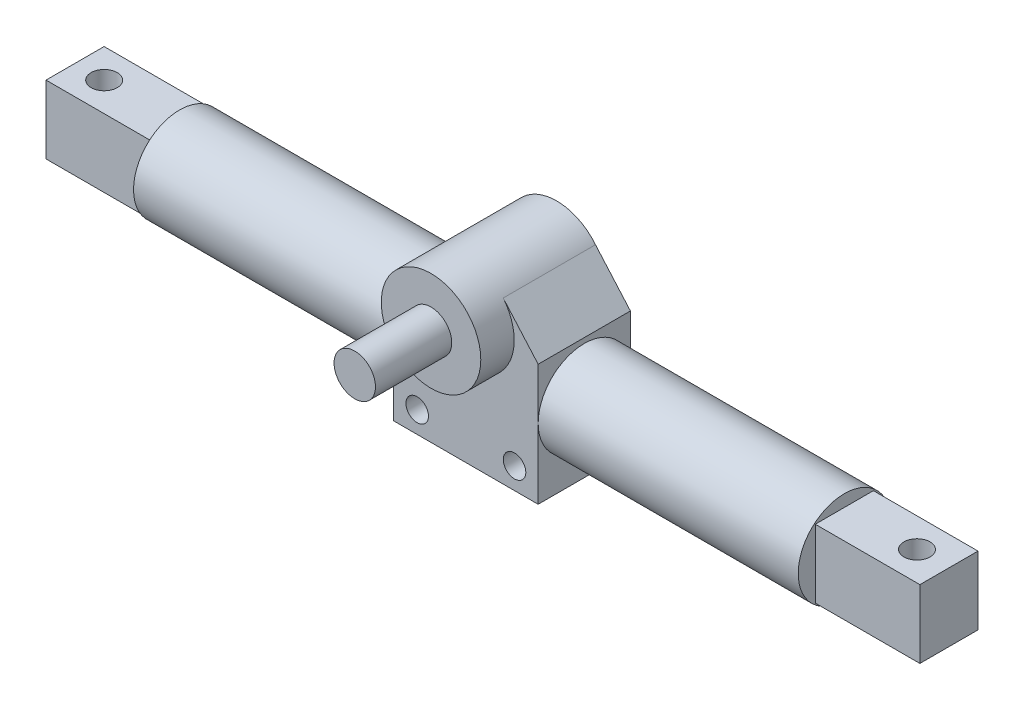
SolidWorks part; units mm, degrees
ref_plane "Front Plane" through (0, 0, 0) normal (0, 0, 1) x (1, 0, 0)
ref_plane "Top Plane" through (0, 0, 0) normal (0, 1, 0) x (1, 0, 0)
ref_plane "Right Plane" through (0, 0, 0) normal (1, 0, 0) x (0, 0, -1)
sketch "Sketch1" plane through (0, 0, 0) normal (0, 0, 1) x (1, 0, 0)
  line L1 (0, 0) -> (50.546, 0)
  line L2 (0, 0) -> (0, 42.418)
  line L3 (0, 42.418) -> (50.546, 42.418)
  line L4 (50.546, 0) -> (50.546, 42.418)
  dimension "D1" = 42.418
  dimension "D2" = 50.546
extrude "Boss-Extrude1" add sketch "Sketch1" along normal blind 32.258
sketch "Sketch2" plane through (0, 0, 32.258) normal (0, 0, 1) x (1, 0, 0)
  line L0 (0, 0) -> (50.546, 0) construction
  line L1 (0, 42.418) -> (11.216, 56.3682)
  line L2 (50.546, 42.418) -> (38.3356, 56.3682)
  line L3 (0, 42.418) -> (50.546, 42.418)
  arc A0 (38.3356, 56.3682) -> (11.216, 56.3682) centre (24.7758, 45.466) ccw
  dimension "D1" = 34.798
  dimension "D3" = 45.466
  dimension "D4" = 13.9502
  dimension "D5" = 13.9502
extrude "Boss-Extrude2" add sketch "Sketch2" against normal blind 32.258
sketch "Sketch3" plane through (0, 0, 0) normal (-1, 0, 0) x (0, 0, 1)
  line L0 (32.258, 42.418) -> (32.258, 0) construction
  line L1 (32.258, 0) -> (0, 0) construction
  circle A0 centre (16.129, 24.511) radius 16.129
  point P4 (0, 0)
  dimension "D2" = 32.258
  dimension "D1" = 16.129
  dimension "D3" = 24.511
extrude "Boss-Extrude3" add sketch "Sketch3" along normal blind 90.932
sketch "Sketch5" plane through (50.546, 0, 0) normal (1, 0, 0) x (0, 0, -1)
  line L0 (0, 0) -> (0, 42.418) construction
  line L1 (-32.258, 0) -> (0, 0) construction
  circle A0 centre (-16.129, 24.511) radius 16.129
  dimension "D1" = 32.258
  dimension "D2" = 16.129
  dimension "D3" = 24.511
extrude "Boss-Extrude4" add sketch "Sketch5" along normal blind 90.932
sketch "Sketch6" plane through (0, 0, 32.258) normal (0, 0, 1) x (1, 0, 0)
  line L0 (50.546, 0) -> (50.546, 24.511) construction
  line L1 (0, 0) -> (50.546, 0) construction
  line L2 (25.273, 0) -> (25.273, 11.6029) construction
  circle A0 centre (42.291, 7.493) radius 3.937
  circle A2 centre (8.255, 7.493) radius 3.937
  dimension "D2" = 7.874
  dimension "D3" = 8.255
  dimension "D4" = 7.493
extrude "Cut-Extrude1" cut sketch "Sketch6" against normal blind 90.932
sketch "Sketch8" plane through (0, 0, 32.258) normal (0, 0, 1) x (1, 0, 0)
  circle A0 centre (24.7758, 45.466) radius 17.399
  dimension "D1" = 34.798
extrude "Boss-Extrude5" add sketch "Sketch8" along normal blind 11.684
sketch "Sketch9" plane through (0, 0, 43.942) normal (0, 0, 1) x (1, 0, 0)
  circle A0 centre (24.7758, 45.466) radius 7.239
  dimension "D1" = 14.478
extrude "Boss-Extrude6" add sketch "Sketch9" along normal blind 26.67
sketch "Sketch10" plane through (141.478, 0, 0) normal (1, 0, 0) x (0, 0, -1)
  line L1 (-26.289, 36.449) -> (-5.969, 36.449)
  line L2 (-26.289, 36.449) -> (-26.289, 12.573)
  line L3 (-26.289, 12.573) -> (-5.969, 12.573)
  line L4 (-5.969, 36.449) -> (-5.969, 12.573)
  line L5 (-26.289, 36.449) -> (-5.969, 12.573) construction
  line L6 (-26.289, 12.573) -> (-5.969, 36.449) construction
  point P0 (-16.129, 24.511)
  dimension "D1" = 23.876
  dimension "D2" = 20.32
extrude "Boss-Extrude7" add sketch "Sketch10" along normal blind 36.576
sketch "Sketch11" plane through (-90.932, 0, 0) normal (-1, 0, 0) x (0, 0, 1)
  line L1 (5.969, 36.449) -> (26.289, 36.449)
  line L2 (5.969, 36.449) -> (5.969, 12.573)
  line L3 (5.969, 12.573) -> (26.289, 12.573)
  line L4 (26.289, 36.449) -> (26.289, 12.573)
  line L5 (5.969, 36.449) -> (26.289, 12.573) construction
  line L6 (5.969, 12.573) -> (26.289, 36.449) construction
  point P0 (16.129, 24.511)
  dimension "D1" = 23.876
  dimension "D2" = 20.32
extrude "Boss-Extrude8" add sketch "Sketch11" along normal blind 36.576
sketch "Sketch12" plane through (0, 36.449, 0) normal (0, 1, 0) x (1, 0, 0)
  line L0 (178.054, -5.969) -> (178.054, -26.289) construction
  line L1 (178.054, -26.289) -> (141.478, -26.289) construction
  line L2 (24.7758, -70.612) -> (24.7758, 20.6139) construction
  line L3 (17.5368, -70.612) -> (32.0148, -70.612) construction
  circle A0 centre (166.878, -16.129) radius 4.572
  circle A1 centre (-117.3263, -16.129) radius 4.572
  dimension "D1" = 9.144
  dimension "D2" = 11.176
  dimension "D3" = 10.16
extrude "Cut-Extrude2" cut sketch "Sketch12" against normal blind 36.576
